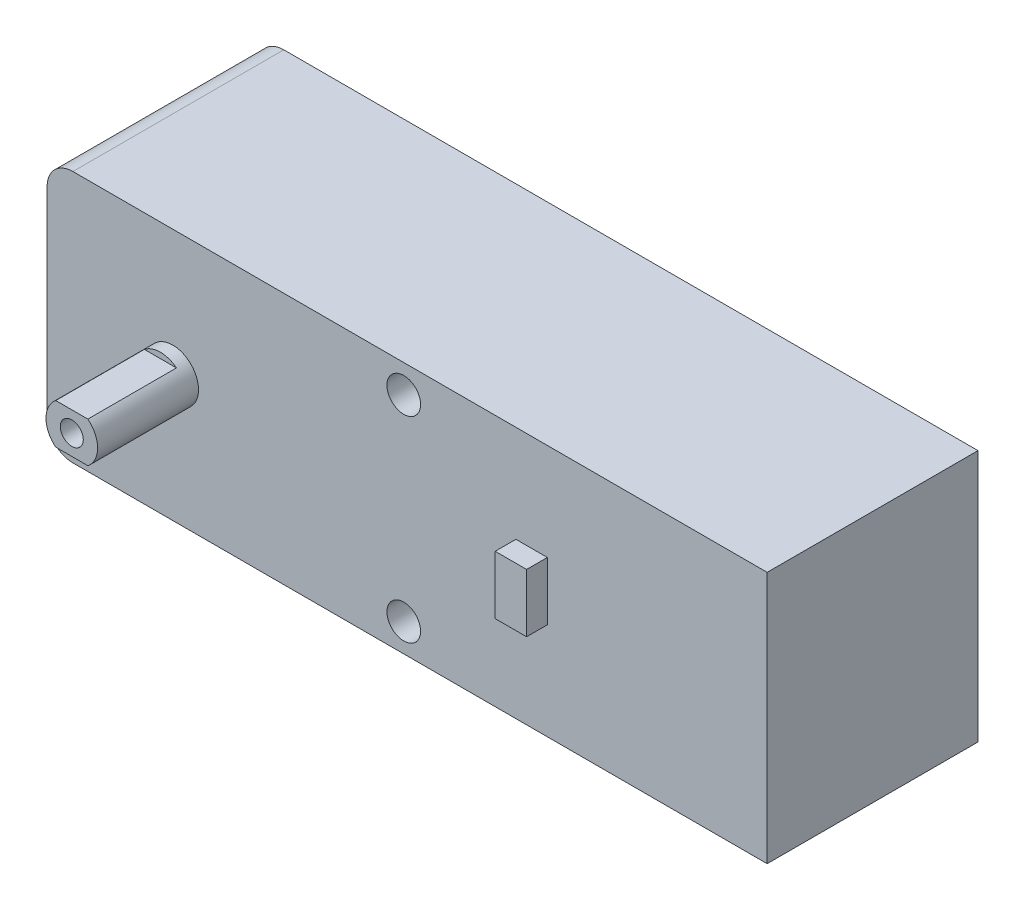
SolidWorks part; units mm, degrees
ref_plane "Plano frontal" through (0, 0, 0) normal (0, 0, 1) x (1, 0, 0)
ref_plane "Plano superior" through (0, 0, 0) normal (0, 1, 0) x (1, 0, 0)
ref_plane "Plano direito" through (0, 0, 0) normal (1, 0, 0) x (0, 0, -1)
sketch "Esboço1" plane through (0, 0, 0) normal (0, 0, 1) x (1, 0, 0)
  line L1 (0, 0) -> (64.2, 0)
  line L2 (0, 0) -> (0, 22.5)
  line L3 (0, 22.5) -> (64.2, 22.5)
  line L4 (64.2, 0) -> (64.2, 22.5)
  dimension "D1" = 22.5
  dimension "D2" = 64.2
extrude "Ressalto-extrusão1" add sketch "Esboço1" along normal mid plane 18.8
sketch "Esboço2" plane through (0, 0, 9.4) normal (0, 0, 1) x (1, 0, 0)
  line L0 (0, 11.25) -> (34.9763, 11.25) construction
  line L1 (0, 22.5) -> (0, 0) construction
  circle A0 centre (11.2, 11.25) radius 2.3
  dimension "D2" = 4.6
  dimension "D1" = 11.2
extrude "Ressalto-extrusão2" add sketch "Esboço2" along normal blind 9
sketch "Esboço3" plane through (0, 0, 18.4) normal (0, 0, 1) x (1, 0, 0)
  line L0 (9.7682, 13.05) -> (12.6318, 13.05)
  line L1 (12.6318, 9.45) -> (9.7682, 9.45)
  line L2 (8.9, 11.25) -> (13.5, 11.25) construction
  circle A0 centre (11.2, 11.25) radius 2.3 construction
  circle A1 centre (11.2, 11.25) radius 2.3 construction
  arc A2 (12.6318, 13.05) -> (9.7682, 13.05) centre (11.2, 11.25) ccw
  arc A3 (9.7682, 9.45) -> (12.6318, 9.45) centre (11.2, 11.25) ccw
  dimension "D1" = 3.6
extrude "Corte-extrusão1" cut sketch "Esboço3" against normal blind 7.9
sketch "Esboço4" plane through (0, 0, 9.4) normal (0, 0, 1) x (1, 0, 0)
  line L0 (31.8, 20) -> (31.8, 2.5) construction
  line L1 (0, 22.5) -> (0, 0) construction
  line L2 (0, 11.25) -> (31.8, 11.25) construction
  circle A0 centre (31.8, 20) radius 1.5
  circle A1 centre (31.8, 2.5) radius 1.5
  dimension "D2" = 3
  dimension "D1" = 31.8
  dimension "D3" = 17.5
extrude "Corte-extrusão2" cut sketch "Esboço4" against normal through all
hole_wizard "Furo roscado de M2.51" positions "Esboço7" profile "Esboço6" tap size "M2.5" standard "ISO"
sketch "Esboço7" plane through (0, 0, 18.4) normal (0, 0, 1) x (1, 0, 0)
  point P0 (11.2, 11.25)
sketch "Esboço6" plane through (11.2, 11.25, 18.4) normal (1, 0, 0) x (0, -1, 0)
  line L0 (0, 0) -> (0, 7.8659)
  line L1 (0, 7.8659) -> (1.025, 7.25)
  line L2 (1.025, 7.25) -> (1.025, 0)
  line L5 (1.025, 0) -> (0, 0)
  line L10 (0, 7.8659) -> (-1.025, 7.25) construction
  line L11 (0, -6.35) -> (0, 107.95) construction
  dimension "Tap Drill Dia." = 2.05
  dimension "Tap Drill Depth" = 7.25
  dimension "Drill Angle" = 118
cosmetic thread "Rosca de furo1" parameters "D1"=5, "D2"=2.5
mirror "Espelhar1" about plane through (0, 0, 0) normal (0, 0, 1) of "Furo roscado de M2.51", "Ressalto-extrusão2", "Corte-extrusão1"
fillet "Filete1" radius 2.3 2 edges at (0, 0, 0) (0, 22.5, 0)
sketch "Esboço5" plane through (0, 0, 9.4) normal (0, 0, 1) x (1, 0, 0)
  line L0 (11.2, 11.25) -> (41.8, 11.25) construction
  line L1 (41.8, 13.85) -> (44.6, 13.85)
  line L2 (41.8, 13.85) -> (41.8, 8.65)
  line L3 (41.8, 8.65) -> (44.6, 8.65)
  line L4 (44.6, 13.85) -> (44.6, 8.65)
  line L5 (0, 20.2) -> (0, 2.3) construction
  dimension "D1" = 5.2
  dimension "D2" = 41.8
  dimension "D3" = 2.8
extrude "Ressalto-extrusão3" add sketch "Esboço5" along normal blind 1.85
